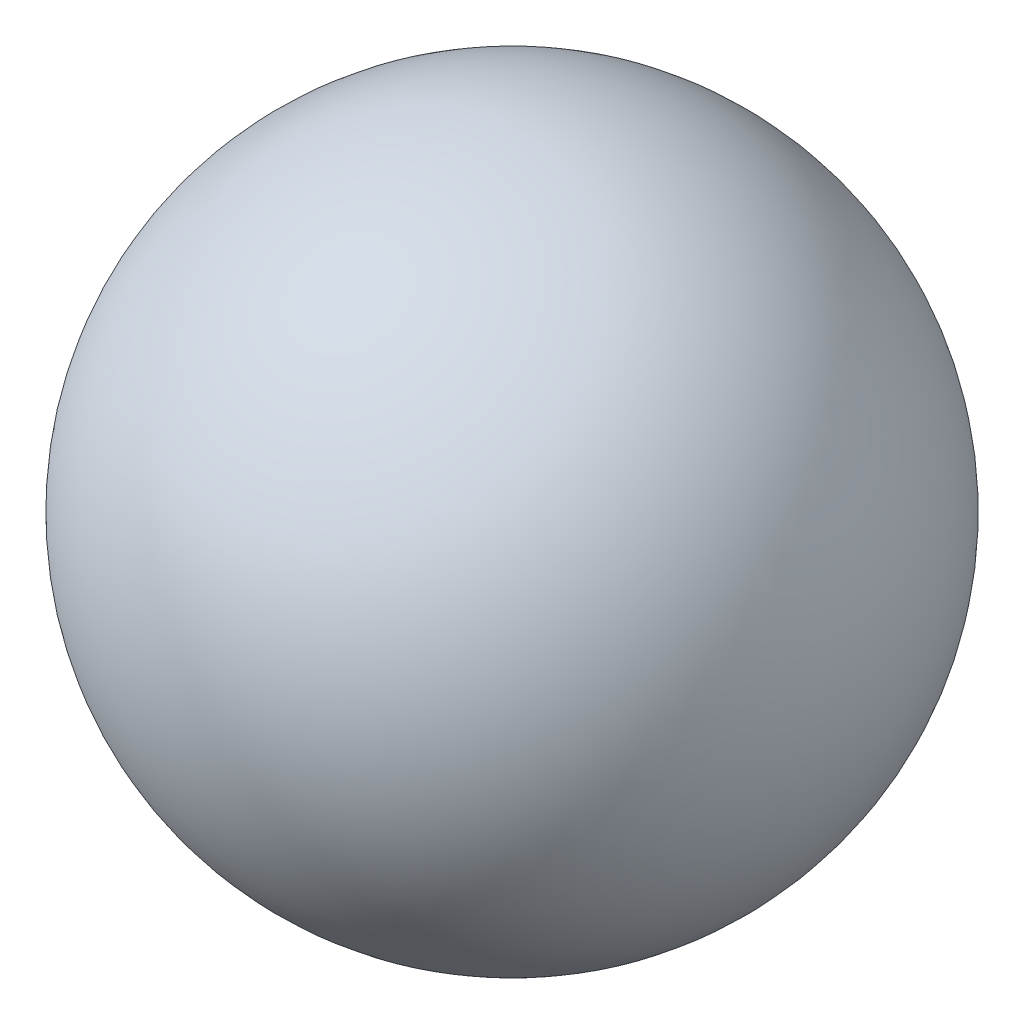
SolidWorks part; units mm, degrees
material "1060 Alloy"
ref_plane "Front" through (0, 0, 0) normal (0, 0, 1) x (1, 0, 0)
ref_plane "Top" through (0, 0, 0) normal (0, 1, 0) x (1, 0, 0)
ref_plane "Right" through (0, 0, 0) normal (1, 0, 0) x (0, 0, -1)
sketch "Çizim1" plane through (0, 0, 0) normal (0, 0, 1) x (1, 0, 0)
  line L0 (0, 1) -> (0, -1) construction
  line L1 (0, 1) -> (0, -1)
  arc A0 (0, -1) -> (0, 1) centre (0, 0) ccw
revolve "Döndür1" add sketch "Çizim1" angle 360 about L0
